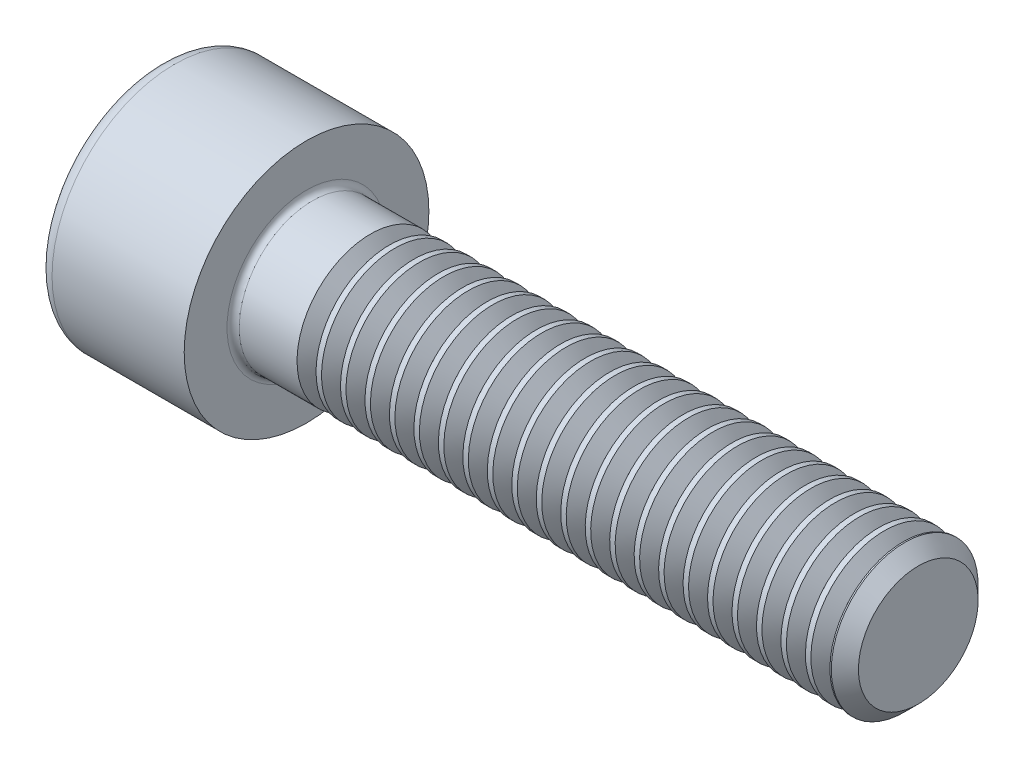
SolidWorks part; units mm, degrees
ref_plane "Plane1" through (0, 0, 0) normal (0, 0, 1) x (1, 0, 0)
ref_plane "Plane2" through (0, 0, 0) normal (0, 1, 0) x (1, 0, 0)
ref_plane "Plane3" through (0, 0, 0) normal (1, 0, 0) x (0, 0, -1)
revolve "Base-Revolve" add sketch "BodySke"
sketch "BodySke" plane through (0, 0, 0) normal (0, 0, 1) x (1, 0, 0)
  line L0 (0, 0) -> (0, 5)
  line L1 (0, 5) -> (6, 5)
  line L2 (6, 5) -> (6, 3)
  line L3 (6, 3) -> (30.4455, 3)
  line L4 (31, 2.4455) -> (31, 0)
  line L5 (31, 0) -> (0, 0)
  line L6 (-31.75, 0) -> (127, 0) construction
  line L8 (31, 2.4455) -> (30.4455, 3)
  line L10 (31, -2.4455) -> (30.4455, -3) construction
  line L11 (7, 9.525) -> (7, 3.175) construction
  line L12 (6, 9.525) -> (6, 3.175) construction
  line L13 (-29, 9.525) -> (-29, 3.175) construction
  dimension "Diameter" = 6
  dimension "Head_ht" = 6
  dimension "Length" = 25
  dimension "Body_ch_ang" = 45
  dimension "Head_dia" = 10
  dimension "Minor_dia" = 4.891
  dimension "Advance" = 1
  dimension "Thread_nom" = 25
  dimension "Thread_length" = 60
cosmetic thread "ThreadCosmetic" [suppressed]
fillet "Fillet1" radius 0.25 1 edges at (6, 0, 3)
fillet "Fillet2" radius 0.6 1 edges at (0, 0, 5)
sketch "Sketch2" plane through (0, 0, 0) normal (0, 0, 1) x (1, 0, 0)
  line L0 (0, 2.51) -> (3, 2.51)
  line L1 (3, 2.51) -> (4.4491, 0)
  line L2 (-31.75, 0) -> (127, 0) construction
  line L3 (4.4491, 0) -> (0, 0)
  line L4 (0, 0) -> (0, 2.51)
  line L6 (0, 0) -> (47.625, 0) construction
  dimension "D1" = 2.51
  dimension "D2" = 60
  dimension "Depth" = 3
revolve "Hex-PreBroach" cut sketch "Sketch2" angle 360 about L6
sketch "Sketch3" plane through (0, 0, 0) normal (-1, 0, 0) x (0, 0.5, 0.866)
  line L0 (1.4491, 2.51) -> (-1.4491, 2.51)
  line L1 (-1.4491, 2.51) -> (-2.8983, 0)
  line L2 (1.4491, 2.51) -> (2.8983, 0)
  line L3 (1.4491, -2.51) -> (2.8983, 0)
  line L4 (1.4491, -2.51) -> (-1.4491, -2.51)
  line L5 (-1.4491, -2.51) -> (-2.8983, 0)
  dimension "D1" = 2.51
  dimension "D2" = 2.51
  dimension "Hex_size" = 5.02
extrude "Hex" cut sketch "Sketch3" against normal blind 3
sketch "ThdSchSke" plane through (0, 0, 0) normal (0, 0, 1) x (1, 0, 0)
  line L0 (9, -2.4455) -> (8.6117, -3)
  line L1 (9, -2.4455) -> (9.3883, -3)
  line L2 (9.3883, -3) -> (9.3883, -3.75)
  line L3 (-3.175, 0) -> (5.1513, 0) construction
  line L4 (0, 4.4) -> (0, -4.4) construction
  line L5 (9.3883, -3.75) -> (8.6117, -3.75)
  line L6 (8.6117, -3.75) -> (8.6117, -3)
  dimension "Thread_minor" = 4.891
  dimension "Diameter" = 6
  dimension "Start" = 9
  dimension "SideAngle" = 55
  dimension "VeeAngle" = 70
  dimension "Overcut" = 7.5
revolve "ThreadSchematic" cut sketch "ThdSchSke" angle 360 about L3
pattern_linear "ThdSchPat" count 22 spacing 1 along (1, 0, 0) of "ThreadSchematic"
equation "\"D2@Sketch3\" = \"Hex_size@Sketch3\" / 2"
equation "\"D1@Sketch3\" = \"Hex_size@Sketch3\" / 2"
equation "\"D1@Sketch2\" = \"Hex_size@Sketch3\" / 2"
equation "\"Thread_minor@ThreadCosmetic\"  =  \"Minor_dia@BodySke\""
equation "\"Depth@Sketch2\" =  \"Key_eng@Hex\""
equation "\"Thread_length@ThreadCosmetic\" = ((sgn( (\"Length@BodySke\" - \"Advance@BodySke\" * 3.0) - \"Thread_nom@BodySke\" )-1)*( (\"Length@BodySke\" - \"Advance@BodySke\" * 3.0) - \"Thread_nom@BodySke\" ))/-2+ \"Thread_nom@BodySke\""
equation "\"Thread_minor@ThdSchSke\" = \"Minor_dia@BodySke\""
equation "\"Diameter@ThdSchSke\" = \"Diameter@BodySke\""
equation "\"Overcut@ThdSchSke\" = \"Diameter@BodySke\" * 1.25"
equation "\"Start@ThdSchSke\" = \"Head_ht@BodySke\" + \"Length@BodySke\" - \"Thread_length@ThreadCosmetic\"  '---Non-countersunk---"
equation "\"Num_threads@ThdSchPat\" = int( \"Thread_length@ThreadCosmetic\" / \"Advance@BodySke\" + 0.999 )  + 1"
equation "\"Advance@ThdSchPat\" = \"Thread_length@ThreadCosmetic\" /  (\"Num_threads@ThdSchPat\" - 1) 'relax it"
equation "\"Num_threads@ThdSchPat\" = \"Num_threads@ThdSchPat\" - sgn( \"Num_threads@ThdSchPat\" - 1) '---chamfered tips only---"
